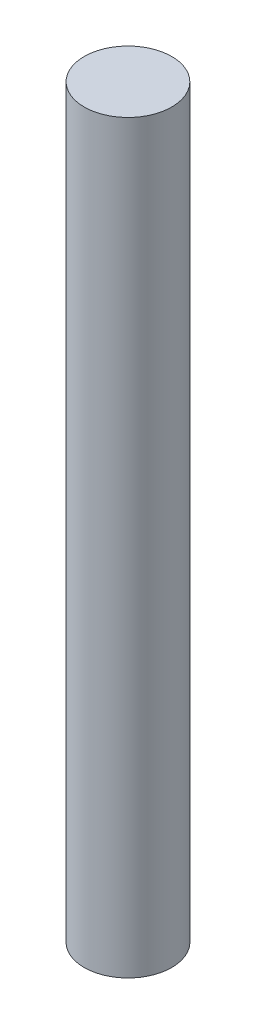
SolidWorks part; units mm, degrees
ref_plane "Alzado" through (0, 0, 0) normal (0, 0, 1) x (1, 0, 0)
ref_plane "Planta" through (0, 0, 0) normal (0, 1, 0) x (1, 0, 0)
ref_plane "Vista lateral" through (0, 0, 0) normal (1, 0, 0) x (0, 0, -1)
sketch "Croquis1" plane through (0, 0, 0) normal (0, 1, 0) x (1, 0, 0)
  circle A0 centre (0, 0) radius 5.975
  dimension "D1" = 11.95
extrude "Saliente-Extruir1" add sketch "Croquis1" along normal blind 101.72
